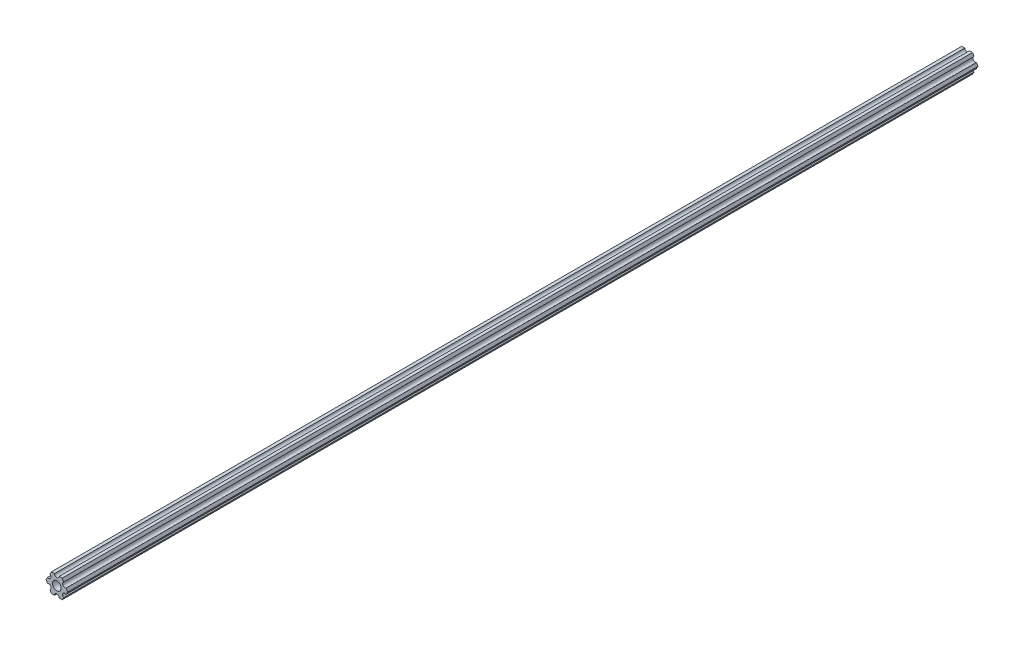
SolidWorks part; units mm, degrees
ref_plane "Front Plane" through (0, 0, 0) normal (0, 0, 1) x (1, 0, 0)
ref_plane "Top Plane" through (0, 0, 0) normal (0, 1, 0) x (1, 0, 0)
ref_plane "Right Plane" through (0, 0, 0) normal (1, 0, 0) x (0, 0, -1)
sketch "Sketch1" plane through (0, 0, 0) normal (0, 0, 1) x (1, 0, 0)
  line L0 (-1.5875, 6.35) -> (-3.6662, 6.35)
  line L1 (7.3323, 0) -> (6.293, 1.8002)
  line L2 (3.6662, 6.35) -> (1.5875, 6.35)
  line L3 (-3.6662, 6.35) -> (-4.7055, 4.5498)
  line L4 (-7.3323, 0) -> (-6.293, -1.8002)
  line L5 (-3.6662, -6.35) -> (-1.5875, -6.35)
  line L6 (3.6662, -6.35) -> (4.7055, -4.5498)
  line L7 (-6.293, 1.8002) -> (-7.3323, 0)
  line L8 (-4.7055, -4.5498) -> (-3.6662, -6.35)
  line L9 (1.5875, -6.35) -> (3.6662, -6.35)
  line L10 (6.293, -1.8002) -> (7.3323, 0)
  line L11 (4.7055, 4.5498) -> (3.6662, 6.35)
  circle A0 centre (0, 0) radius 2.9337
  arc A2 (-1.5875, 6.35) -> (1.5875, 6.35) centre (0, 6.35) ccw
  arc A3 (4.7055, 4.5498) -> (6.293, 1.8002) centre (5.4993, 3.175) ccw
  arc A4 (6.293, -1.8002) -> (4.7055, -4.5498) centre (5.4993, -3.175) ccw
  arc A5 (1.5875, -6.35) -> (-1.5875, -6.35) centre (0, -6.35) ccw
  arc A6 (-4.7055, -4.5498) -> (-6.293, -1.8002) centre (-5.4993, -3.175) ccw
  arc A7 (-6.293, 1.8002) -> (-4.7055, 4.5498) centre (-5.4993, 3.175) ccw
  dimension "D1" = 5.8674
  dimension "D3" = 3.175
  dimension "D4" = 6
extrude "Boss-Extrude1" add sketch "Sketch1" along normal blind 615.95
